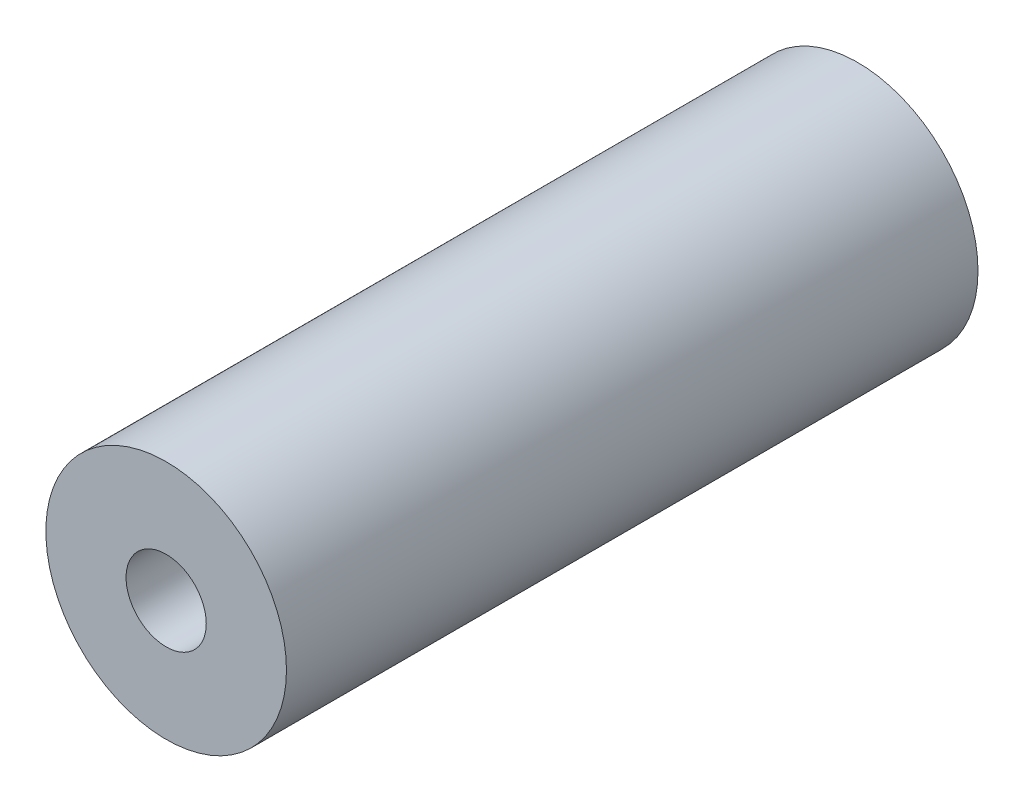
SolidWorks part; units mm, degrees
ref_plane "Front Plane" through (0, 0, 0) normal (0, 0, 1) x (1, 0, 0)
ref_plane "Top Plane" through (0, 0, 0) normal (0, 1, 0) x (1, 0, 0)
ref_plane "Right Plane" through (0, 0, 0) normal (1, 0, 0) x (0, 0, -1)
sketch "Sketch1" plane through (0, 0, 0) normal (0, 0, 1) x (1, 0, 0)
  circle A0 centre (0, 0) radius 19.05
  circle A1 centre (0, 0) radius 6.35
  dimension "D1" = 12.7
  dimension "D2" = 38.1
extrude "Boss-Extrude1" add sketch "Sketch1" along normal mid plane 109.5
